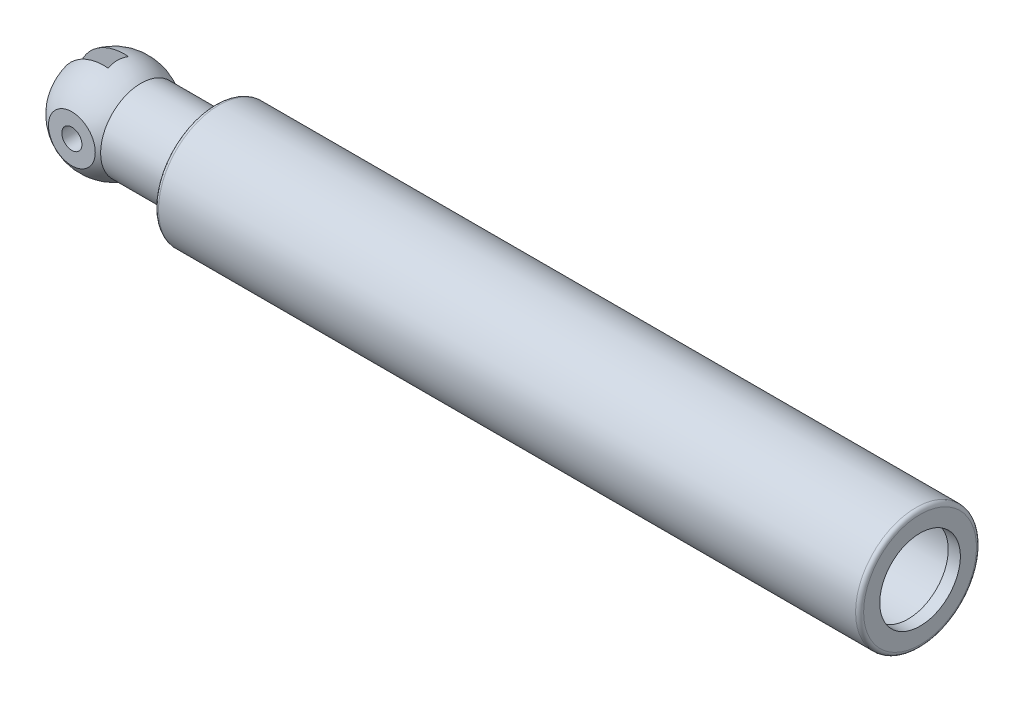
SolidWorks part; units mm, degrees
ref_plane "Front Plane" through (0, 0, 0) normal (0, 0, 1) x (1, 0, 0)
ref_plane "Top Plane" through (0, 0, 0) normal (0, 1, 0) x (1, 0, 0)
ref_plane "Right Plane" through (0, 0, 0) normal (1, 0, 0) x (0, 0, -1)
sketch "Sketch1" plane through (0, 0, 0) normal (0, 0, 1) x (1, 0, 0)
  line L0 (172, 10) -> (175, 10)
  line L1 (0, 0) -> (3, 0)
  line L2 (0, 10) -> (0, 15)
  line L3 (0, 15) -> (175, 15)
  line L4 (175, 10) -> (175, 15)
  line L6 (3, 0) -> (3, 12)
  line L7 (3, 12) -> (172, 12)
  line L8 (172, 10) -> (172, 12)
  line L12 (0, 10) -> (-18.3668, 10)
  line L13 (-37, 0) -> (0, 0)
  arc A0 (-18.3668, 10) -> (-37, 0) centre (-25, 0) ccw
  dimension "D10" = 12
  dimension "D11" = 25
  dimension "D1" = 175
  dimension "D2" = 15
  dimension "D3" = 3
  dimension "D4" = 3
  dimension "D5" = 3
  dimension "D6" = 10
  dimension "D7" = 10
revolve "Revolve1" add sketch "Sketch1" angle 360 about L1
sketch "Sketch4" plane through (0, 0, 0) normal (0, 1, 0) x (1, 0, 0)
  line L0 (-19.5, 2.5) -> (-19.5, -2.5)
  line L1 (-19.5, 2.5) -> (-37, 2.5)
  line L3 (-19.5, -2.5) -> (-37, -2.5)
  line L4 (-37, 2.5) -> (-37, -2.5)
  arc A0 (-18.3668, 10) -> (-18.3668, -10) centre (-25, 0) ccw construction
  point P9 (-37, 0)
  dimension "D1" = 5
  dimension "D2" = 17.5
sketch "Sketch6" plane through (0, 0, 0) normal (-1, 0, 0) x (0, 0, 1)
  line L1 (-10.5, 15) -> (10.5, 15)
  line L2 (-10.5, 15) -> (-10.5, -15)
  line L3 (-10.5, -15) -> (10.5, -15)
  line L4 (10.5, 15) -> (10.5, -15)
  line L5 (0, 15) -> (0, -15) construction
  point P4 (0, 15)
  point P11 (0, 0)
  dimension "D1" = 10.5
  dimension "D2" = 30
extrude "Cut-Extrude3" cut sketch "Sketch6" along normal blind 40 flip side to cut
revolve "Cut-Revolve1" cut sketch "Sketch4" angle 360 about L4
fillet "Fillet1" radius 1 4 edges at (0, 0, 10) (175, 0, 15) (0, 0, -15) (0, 0, 15)
sketch "Sketch7" plane through (0, 0, 0) normal (0, 0, 1) x (1, 0, 0)
  line L0 (3, 0) -> (152, 0) construction
  line L3 (172, 10) -> (172, 12) construction
  dimension "D1" = 20
sketch "Sketch8" plane through (0, 0, 10.5) normal (0, 0, 1) x (1, 0, 0)
  circle A0 centre (-25, 0) radius 2.5
  dimension "D1" = 5
extrude "Cut-Extrude4" cut sketch "Sketch8" against normal through all both and the other way through all
